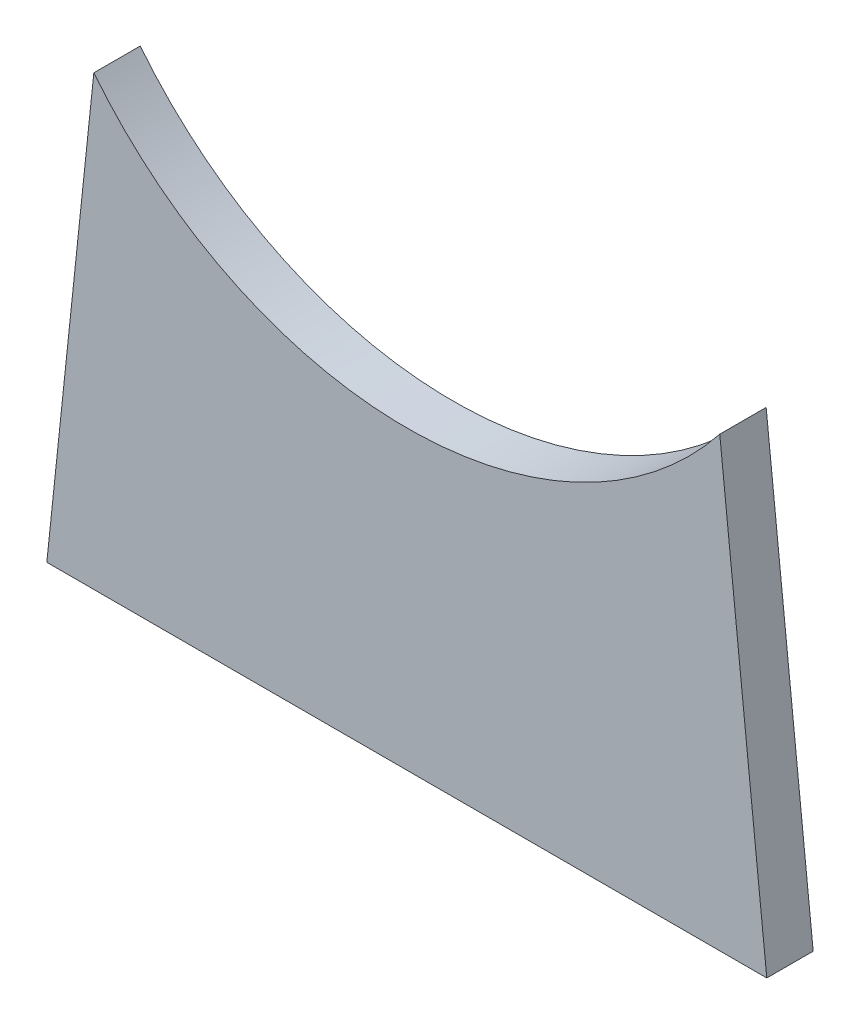
SolidWorks part; units mm, degrees
ref_plane "Front Plane" through (0, 0, 0) normal (0, 0, 1) x (1, 0, 0)
ref_plane "Top Plane" through (0, 0, 0) normal (0, 1, 0) x (1, 0, 0)
ref_plane "Right Plane" through (0, 0, 0) normal (1, 0, 0) x (0, 0, -1)
sketch "Sketch1" plane through (0, 0, 0) normal (0, 0, 1) x (1, 0, 0)
  line L0 (0, 3824.4435) -> (0, 0) construction
  line L1 (-1978.13, 0) -> (1978.13, 0)
  line L2 (1978.13, 0) -> (1719.705, 2458.75)
  line L3 (-1978.13, 0) -> (-1719.705, 2458.75)
  arc A0 (-1719.705, 2458.75) -> (1719.705, 2458.75) centre (0, 3824.4435) ccw
  dimension "D1" = 3956.26
  dimension "D4" = 2196.02
  dimension "D2" = 84
  dimension "D3" = 2458.75
extrude "Boss-Extrude1" add sketch "Sketch1" along normal mid plane 255
